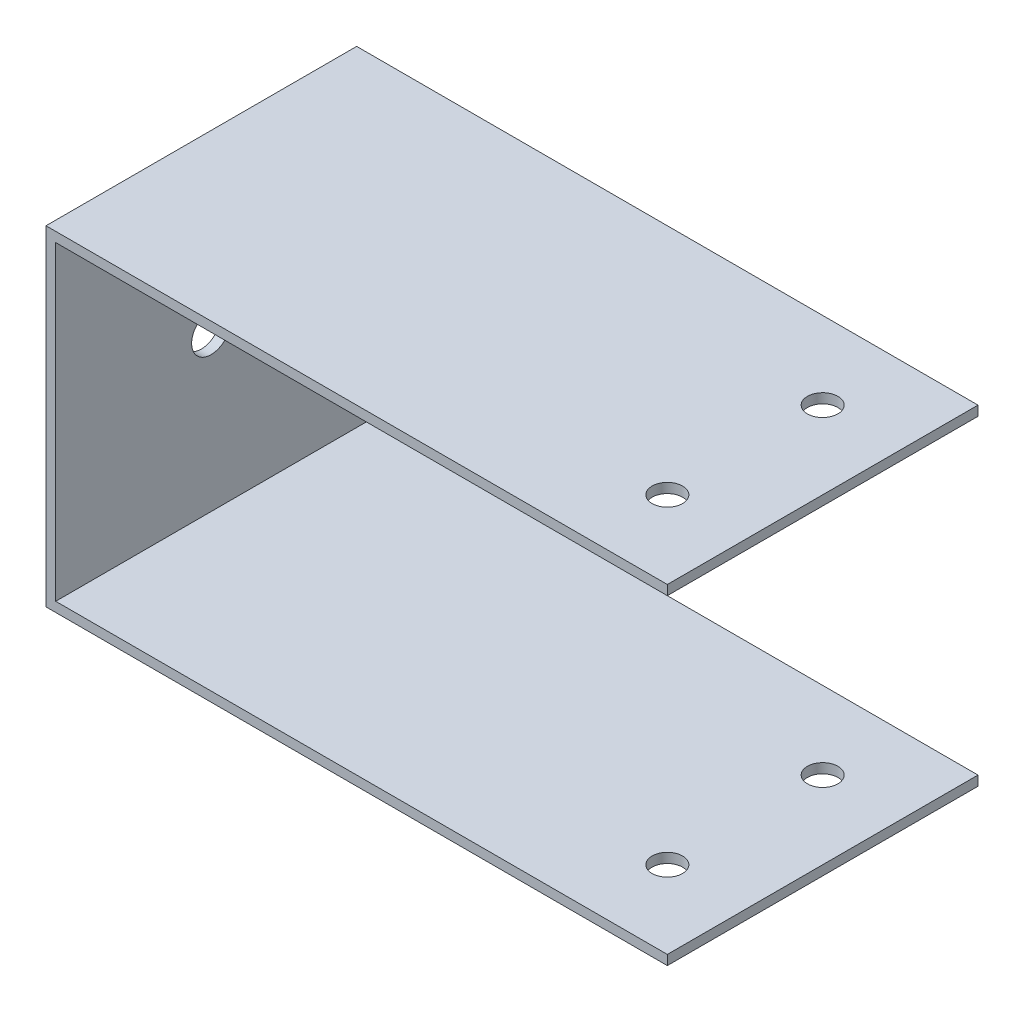
SolidWorks part; units mm, degrees
ref_plane "Front" through (0, 0, 0) normal (0, 0, 1) x (1, 0, 0)
ref_plane "Top" through (0, 0, 0) normal (0, 1, 0) x (1, 0, 0)
ref_plane "Right" through (0, 0, 0) normal (1, 0, 0) x (0, 0, -1)
sketch "Sketch2" plane through (0, 0, 0) normal (0, 0, 1) x (1, 0, 0)
  line L0 (-1.5875, -1.5875) -> (100.0125, -1.5875)
  line L1 (0, 0) -> (100.0125, 0)
  line L2 (0, 0) -> (0, 50.8)
  line L3 (0, 50.8) -> (100.0125, 50.8)
  line L4 (100.0125, 0) -> (100.0125, 50.8) construction
  line L5 (-1.5875, -1.5875) -> (-1.5875, 52.3875)
  line L6 (-1.5875, 52.3875) -> (100.0125, 52.3875)
  line L7 (100.0125, -1.5875) -> (100.0125, 0)
  line L8 (100.0125, 50.8) -> (100.0125, 52.3875)
  dimension "D1" = 50.8
  dimension "D2" = 100.0125
  dimension "D3" = 1.5875
extrude "Boss-Extrude1" add sketch "Sketch2" along normal blind 50.8
sketch "Sketch3" plane through (0, 52.3875, 0) normal (0, 1, 0) x (1, 0, 0)
  line L0 (87.3125, 0) -> (87.3125, -50.8) construction
  line L1 (100.0125, 0) -> (-1.5875, 0) construction
  line L2 (100.0125, -50.8) -> (-1.5875, -50.8) construction
  line L3 (100.0125, -50.8) -> (100.0125, 0) construction
  circle A0 centre (87.3125, -38.1) radius 2.4892
  circle A1 centre (87.3125, -12.7) radius 2.4892
  dimension "D1" = 25.4
  dimension "D2" = 4.9784
  dimension "D3" = 12.7
  dimension "D4" = 12.7
extrude "Cut-Extrude1" cut sketch "Sketch3" against normal through all
sketch "Sketch4" plane through (0, 0, 0) normal (1, 0, 0) x (0, 0, -1)
  line L0 (-25.4, 50.8) -> (-25.4, 0) construction
  line L1 (-50.8, 50.8) -> (0, 50.8) construction
  line L2 (-50.8, 0) -> (0, 0) construction
  circle A0 centre (-25.4, 25.4) radius 3.175
  dimension "D1" = 6.35
extrude "Cut-Extrude2" cut sketch "Sketch4" against normal through all
